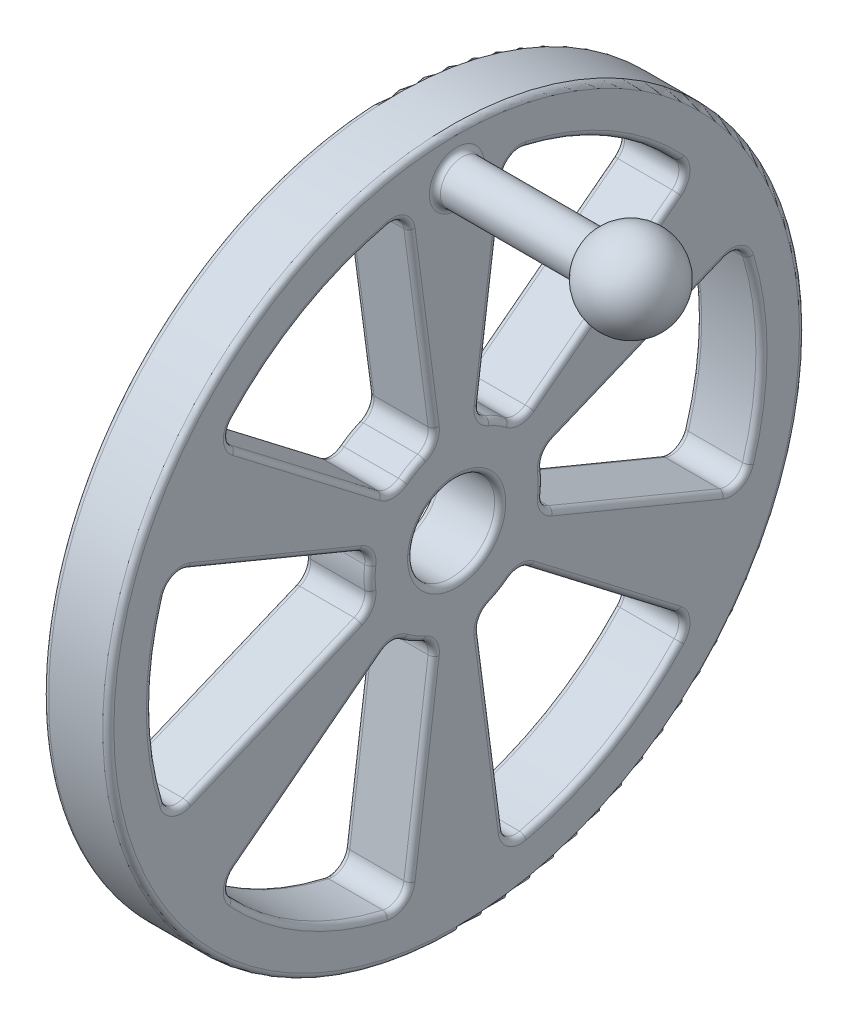
SolidWorks part; units mm, degrees
ref_plane "Front" through (0, 0, 0) normal (0, 0, 1) x (1, 0, 0)
ref_plane "Top" through (0, 0, 0) normal (0, 1, 0) x (1, 0, 0)
ref_plane "Right" through (0, 0, 0) normal (1, 0, 0) x (0, 0, -1)
sketch "Sketch1" plane through (0, 0, 0) normal (1, 0, 0) x (0, 0, -1)
  line L0 (14.1432, 4.2931) -> (39.0976, 14.6296)
  line L3 (14.1432, -4.2931) -> (39.0976, -14.6296)
  line L22 (0, 0) -> (64.1203, 0) construction
  line L24 (10.7895, -10.1018) -> (32.2184, -26.5448)
  line L25 (3.3536, -14.3949) -> (6.8792, -41.1743)
  line L26 (-3.3536, -14.3949) -> (-6.8792, -41.1743)
  line L27 (-10.7895, -10.1018) -> (-32.2184, -26.5448)
  line L28 (-14.1432, -4.2931) -> (-39.0976, -14.6296)
  line L29 (-14.1432, 4.2931) -> (-39.0976, 14.6296)
  line L30 (-10.7895, 10.1018) -> (-32.2184, 26.5448)
  line L31 (-3.3536, 14.3949) -> (-6.8792, 41.1743)
  line L32 (3.3536, 14.3949) -> (6.8792, 41.1743)
  line L33 (10.7895, 10.1018) -> (32.2184, 26.5448)
  circle A126 centre (0, 0) radius 6.35
  arc A131 (12.596, -1.622) -> (12.596, 1.622) centre (0, 0) ccw
  arc A132 (42.4981, -13.0274) -> (42.4981, 13.0274) centre (0, 0) ccw
  circle A133 centre (0, 0) radius 50.8
  arc A134 (39.0976, -14.6296) -> (42.4981, -13.0274) centre (40.0697, -12.2829) ccw
  arc A135 (39.0976, 14.6296) -> (42.4981, 13.0274) centre (40.0697, 12.2829) cw
  arc A136 (12.596, 1.622) -> (14.1432, 4.2931) centre (15.1152, 1.9465) cw
  arc A137 (12.596, -1.622) -> (14.1432, -4.2931) centre (15.1152, -1.9465) ccw
  arc A138 (4.8933, -11.7195) -> (7.7027, -10.0974) centre (0, 0) ccw
  arc A139 (4.8933, -11.7195) -> (3.3536, -14.3949) centre (5.8719, -14.0634) ccw
  arc A140 (7.7027, -10.0974) -> (10.7895, -10.1018) centre (9.2433, -12.1169) cw
  arc A141 (6.8792, -41.1743) -> (9.967, -43.3181) centre (9.3975, -40.8428) ccw
  arc A142 (9.967, -43.3181) -> (32.5311, -30.2908) centre (0, 0) ccw
  arc A143 (32.2184, -26.5448) -> (32.5311, -30.2908) centre (30.6722, -28.5599) cw
  arc A144 (-7.7027, -10.0974) -> (-4.8933, -11.7195) centre (0, 0) ccw
  arc A145 (-7.7027, -10.0974) -> (-10.7895, -10.1018) centre (-9.2433, -12.1169) ccw
  arc A146 (-4.8933, -11.7195) -> (-3.3536, -14.3949) centre (-5.8719, -14.0634) cw
  arc A147 (-32.2184, -26.5448) -> (-32.5311, -30.2908) centre (-30.6722, -28.5599) ccw
  arc A148 (-32.5311, -30.2908) -> (-9.967, -43.3181) centre (0, 0) ccw
  arc A149 (-6.8792, -41.1743) -> (-9.967, -43.3181) centre (-9.3975, -40.8428) cw
  arc A150 (-12.596, 1.622) -> (-12.596, -1.622) centre (0, 0) ccw
  arc A151 (-12.596, 1.622) -> (-14.1432, 4.2931) centre (-15.1152, 1.9465) ccw
  arc A152 (-12.596, -1.622) -> (-14.1432, -4.2931) centre (-15.1152, -1.9465) cw
  arc A153 (-39.0976, 14.6296) -> (-42.4981, 13.0274) centre (-40.0697, 12.2829) ccw
  arc A154 (-42.4981, 13.0274) -> (-42.4981, -13.0274) centre (0, 0) ccw
  arc A155 (-39.0976, -14.6296) -> (-42.4981, -13.0274) centre (-40.0697, -12.2829) cw
  arc A156 (-4.8933, 11.7195) -> (-7.7027, 10.0974) centre (0, 0) ccw
  arc A157 (-4.8933, 11.7195) -> (-3.3536, 14.3949) centre (-5.8719, 14.0634) ccw
  arc A158 (-7.7027, 10.0974) -> (-10.7895, 10.1018) centre (-9.2433, 12.1169) cw
  arc A159 (-6.8792, 41.1743) -> (-9.967, 43.3181) centre (-9.3975, 40.8428) ccw
  arc A160 (-9.967, 43.3181) -> (-32.5311, 30.2908) centre (0, 0) ccw
  arc A161 (-32.2184, 26.5448) -> (-32.5311, 30.2908) centre (-30.6722, 28.5599) cw
  arc A162 (7.7027, 10.0974) -> (4.8933, 11.7195) centre (0, 0) ccw
  arc A163 (7.7027, 10.0974) -> (10.7895, 10.1018) centre (9.2433, 12.1169) ccw
  arc A164 (4.8933, 11.7195) -> (3.3536, 14.3949) centre (5.8719, 14.0634) cw
  arc A165 (32.2184, 26.5448) -> (32.5311, 30.2908) centre (30.6722, 28.5599) ccw
  arc A166 (32.5311, 30.2908) -> (9.967, 43.3181) centre (0, 0) ccw
  arc A167 (6.8792, 41.1743) -> (9.967, 43.3181) centre (9.3975, 40.8428) cw
  point P7 (0, 0)
  point P15 (12.2103, 3.4925)
  point P18 (12.2103, -3.4925)
  point P82 (0, 0)
  dimension "D1" = 101.6
  dimension "D2" = 22.5
  dimension "D3" = 22.5
  dimension "D4" = 12.7
  dimension "D7" = 12.7
  dimension "D8" = 2.54
  dimension "D6" = 44.45
  dimension "D5" = 6.985
extrude "Boss-Extrude2" add sketch "Sketch1" along normal mid plane 9.525
sketch "Sketch2" plane through (0, 0, 0) normal (0, 0, 1) x (1, 0, 0)
  line L0 (4.7625, 47.625) -> (24.6632, 47.625)
  line L1 (4.7625, -50.8) -> (4.7625, 50.8) construction
  line L3 (36.5125, 44.45) -> (4.7625, 44.45)
  line L4 (4.7625, 44.45) -> (4.7625, 47.625)
  arc A0 (36.5125, 44.45) -> (24.6632, 47.625) centre (30.1625, 44.45) ccw
  dimension "D3" = 6.35
  dimension "D1" = 3.175
  dimension "D2" = 31.75
  dimension "D4" = 44.45
revolve "Revolve1" add sketch "Sketch2" angle 360 about L3
fillet "Fillet1" radius 0.8128 101 edges at (-4.7625, -42.9293, -7.9489) (-4.7625, -27.7846, -5.1164) (-4.7625, -12.7965, -3.6704) (-4.7625, -10.9985, -6.35) (-4.7625, -9.5769, -9.2469) (-4.7625, -18.3233, -21.504) (-4.7625, -28.3486, -33.2034) (-4.7625, -42.9293, 7.9489) (-4.7625, -38.4948, 22.225) (-4.7625, -28.3486, 33.2034) (-4.7625, -18.3233, 21.504) (-4.7625, -9.5769, 9.2469) (-4.7625, -10.9985, 6.35) (-4.7625, -12.7965, 3.6704) (4.7625, -9.5769, 9.2469) (4.7625, -10.9985, 6.35) (4.7625, -12.7965, 3.6704) (4.7625, -27.7846, 5.1164) (4.7625, -42.9293, 7.9489) (4.7625, -38.4948, 22.225) (4.7625, -28.3486, 33.2034) (-4.7625, 3.2196, 12.9173) (-4.7625, 0, 12.7) (-4.7625, -3.2196, 12.9173) (-4.7625, -9.4613, 26.6204) (-4.7625, -14.5806, 41.1523) (-4.7625, 0, 44.45) (-4.7625, 14.5806, 41.1523) (4.7625, 3.2196, 12.9173) (4.7625, 0, 12.7) (4.7625, -3.2196, 12.9173) (4.7625, -9.4613, 26.6204) (4.7625, -14.5806, 41.1523) (4.7625, 0, 44.45) (4.7625, 14.5806, 41.1523) (4.7625, 12.7965, 3.6704) (4.7625, 10.9985, 6.35) (4.7625, 9.5769, 9.2469) (4.7625, 18.3233, 21.504) (4.7625, 28.3486, 33.2034) (4.7625, 38.4948, 22.225) (4.7625, 42.9293, 7.9489) (-4.7625, 12.7965, 3.6704) (-4.7625, 10.9985, 6.35) (-4.7625, 9.5769, 9.2469) (-4.7625, 18.3233, 21.504) (-4.7625, 28.3486, 33.2034) (-4.7625, 38.4948, 22.225) (-4.7625, 42.9293, 7.9489) (-4.7625, 9.5769, -9.2469) (-4.7625, 10.9985, -6.35) (-4.7625, 12.7965, -3.6704) (-4.7625, 27.7846, -5.1164) (-4.7625, 42.9293, -7.9489) (-4.7625, 38.4948, -22.225) (-4.7625, 28.3486, -33.2034) (-4.7625, -14.5806, -41.1523) (-4.7625, -9.4613, -26.6204) (-4.7625, -3.2196, -12.9173) (-4.7625, 0, -12.7) (-4.7625, 3.2196, -12.9173) (-4.7625, 9.4613, -26.6204) (-4.7625, 14.5806, -41.1523) (4.7625, -28.3486, -33.2034) (4.7625, -38.4948, -22.225) (4.7625, -42.9293, -7.9489) (4.7625, -27.7846, -5.1164) (4.7625, -12.7965, -3.6704) (4.7625, -10.9985, -6.35) (4.7625, -9.5769, -9.2469) (4.7625, 14.5806, -41.1523) (4.7625, 0, -44.45) (4.7625, -14.5806, -41.1523) (4.7625, -9.4613, -26.6204) (4.7625, -3.2196, -12.9173) (4.7625, 0, -12.7) (4.7625, 3.2196, -12.9173) (4.7625, 9.5769, -9.2469) (4.7625, 10.9985, -6.35) (4.7625, 12.7965, -3.6704) (4.7625, 27.7846, -5.1164) (4.7625, 42.9293, -7.9489) (4.7625, 38.4948, -22.225) (4.7625, 28.3486, -33.2034) (-4.7625, 0, -50.8) (-4.7625, -38.4948, -22.225) (4.7625, 0, -50.8) (4.7625, 0, -6.35) (-4.7625, 0, -6.35) (-4.7625, -27.7846, 5.1164) (4.7625, -18.3233, 21.504) (-4.7625, 9.4613, 26.6204) (4.7625, 9.4613, 26.6204) (4.7625, 27.7846, 5.1164) (-4.7625, 27.7846, 5.1164) (-4.7625, 18.3233, -21.504) (-4.7625, 0, -44.45) (4.7625, -18.3233, -21.504) (4.7625, 9.4613, -26.6204) (4.7625, 18.3233, -21.504) (4.7625, 44.45, -3.175)
